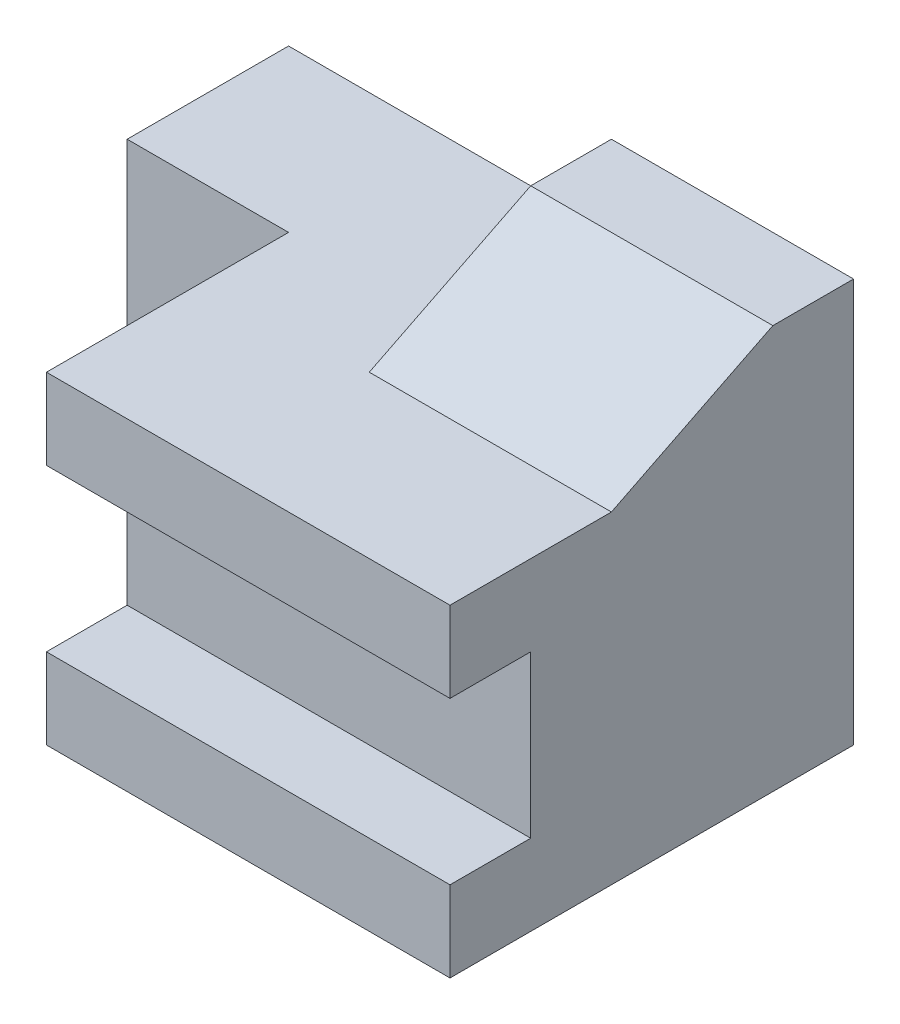
SolidWorks part; units mm, degrees
ref_plane "Front Plane" through (0, 0, 0) normal (0, 0, 1) x (1, 0, 0)
ref_plane "Top Plane" through (0, 0, 0) normal (0, 1, 0) x (1, 0, 0)
ref_plane "Right Plane" through (0, 0, 0) normal (1, 0, 0) x (0, 0, -1)
sketch "Sketch1" plane through (0, 0, 0) normal (0, 0, 1) x (1, 0, 0)
  line L1 (0, 0) -> (70, 0)
  line L2 (0, 0) -> (0, 40)
  line L3 (0, 40) -> (70, 40)
  line L4 (70, 0) -> (70, 40)
  dimension "D1" = 40
  dimension "D2" = 70
extrude "Boss-Extrude1" add sketch "Sketch1" along normal blind 50
sketch "Sketch2" plane through (0, 40, 0) normal (0, 1, 0) x (1, 0, 0)
  line L1 (0, -50) -> (20, -50)
  line L2 (0, -50) -> (0, -20)
  line L3 (0, -20) -> (20, -20)
  line L4 (20, -50) -> (20, -20)
  dimension "D1" = 20
  dimension "D2" = 20
extrude "Cut-Extrude1" cut sketch "Sketch2" against normal blind 50
sketch "Sketch3" plane through (20, 0, 0) normal (-1, 0, 0) x (0, 0, 1)
  line L0 (50, 40) -> (50, 0) construction
  line L1 (50, 30) -> (40, 30)
  line L2 (50, 30) -> (50, 10)
  line L3 (50, 10) -> (40, 10)
  line L4 (40, 30) -> (40, 10)
  dimension "D1" = 10
  dimension "D2" = 20
  dimension "D3" = 10
extrude "Cut-Extrude2" cut sketch "Sketch3" against normal blind 50
sketch "Sketch4" plane through (0, 40, 0) normal (0, 1, 0) x (1, 0, 0)
  line L1 (70, 0) -> (40, 0)
  line L2 (70, 0) -> (70, -30)
  line L3 (70, -30) -> (40, -30)
  line L4 (40, 0) -> (40, -30)
  dimension "D1" = 30
  dimension "D2" = 30
extrude "Boss-Extrude2" add sketch "Sketch4" along normal blind 10
sketch "Sketch5" plane through (40, 0, 0) normal (-1, 0, 0) x (0, 0, 1)
  line L0 (10, 50) -> (30, 40)
  line L1 (0, 50) -> (30, 50) construction
  line L2 (30, 40) -> (30, 50)
  line L3 (30, 50) -> (10, 50)
  dimension "D1" = 10
extrude "Cut-Extrude3" cut sketch "Sketch5" against normal blind 56
